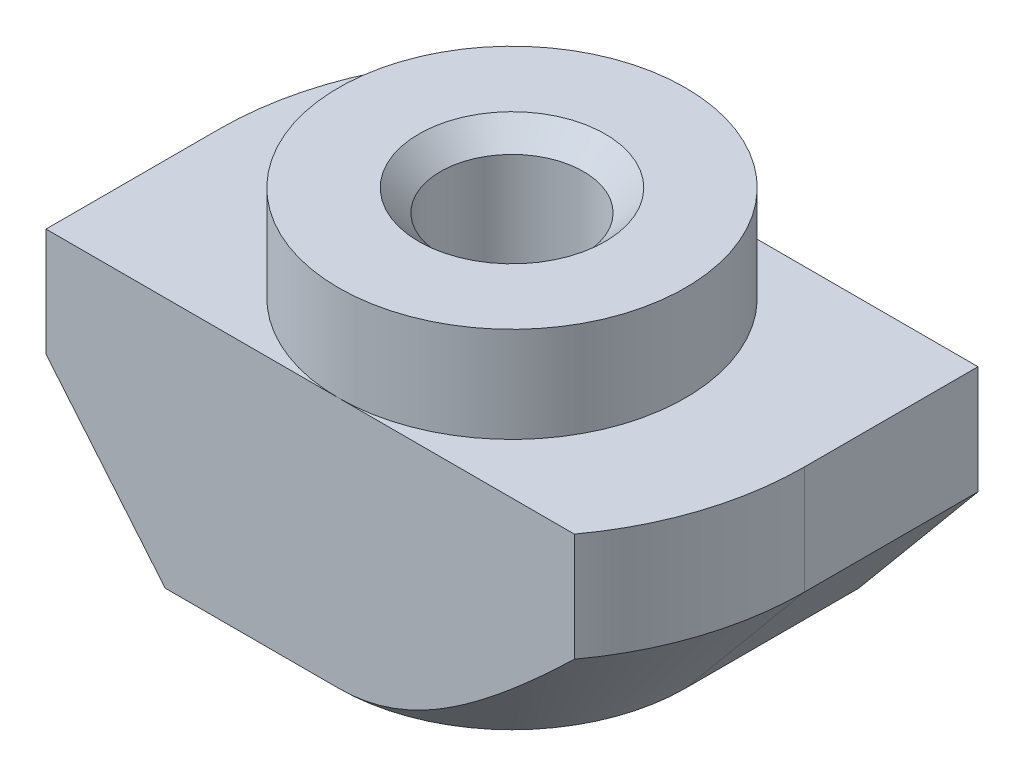
SolidWorks part; units mm, degrees
material "Сталь 20  ГОСТ 1050-2013"
ref_plane "Спереди" through (0, 0, 0) normal (0, 0, 1) x (1, 0, 0)
ref_plane "Сверху" through (0, 0, 0) normal (0, 1, 0) x (1, 0, 0)
ref_plane "Справа" through (0, 0, 0) normal (1, 0, 0) x (0, 0, -1)
sketch "Эскиз1" plane through (0, 0, 0) normal (0, 0, 1) x (1, 0, 0)
  line L0 (4, 0) -> (-4, 0)
  line L1 (-4, 0) -> (-4, -2.2)
  line L2 (-4, -2.2) -> (-6.75, -2.2)
  line L3 (-6.75, -2.2) -> (-6.75, -8)
  line L4 (-6.75, -8) -> (6.75, -8)
  line L5 (0, -8) -> (0, 0) construction
  line L6 (6.75, -2.2) -> (6.75, -8)
  line L7 (4, -2.2) -> (6.75, -2.2)
  line L8 (4, 0) -> (4, -2.2)
  dimension "D1" = 8
  dimension "D2" = 13.5
  dimension "D3" = 8
  dimension "D4" = 2.2
extrude "Бобышка-Вытянуть1" add sketch "Эскиз1" along normal mid plane 8
hole_wizard "Отверстие обработанное метчиком M41" positions "Эскиз2" profile "Эскиз3" tap size "M4" standard "ISO" end condition up to next
sketch "Эскиз2" plane through (0, 0, 0) normal (0, 1, 0) x (1, 0, 0)
  point P0 (0, 0)
sketch "Эскиз3" plane through (0, 0, 0) normal (1, 0, 0) x (0, 0, 1)
  line L0 (0, 0) -> (0, 8)
  line L1 (0, 8) -> (2.15, 8)
  line L2 (1.65, 7.5) -> (1.65, 0.5)
  line L3 (1.65, 0.5) -> (2.15, 0)
  line L5 (2.15, 0) -> (0, 0)
  line L6 (-1.65, 0.5) -> (-2.15, 0) construction
  line L7 (2.15, 8) -> (1.65, 7.5)
  line L8 (-2.15, 8) -> (-1.65, 7.5) construction
  line L11 (0, -6.35) -> (0, 107.95) construction
  dimension "Диаметр проходного сверла" = 3.3
  dimension "Глубина проходного сверла" = 8
  dimension "Диаметр передней зенковки" = 4.3
  dimension "Угол передней зенковки" = 90
  dimension "Диаметр задней зенковки" = 4.3
  dimension "Угол задней зенковки" = 90
cosmetic thread "Отверстие резьбы2" parameters "D2"=4
sketch "Эскиз4" plane through (0, 0, 0) normal (0, 1, 0) x (1, 0, 0)
  line L8 (-4, -4) -> (-4, 4) construction
  circle A2 centre (0, 0) radius 4
extrude "Вырез-Вытянуть1" cut sketch "Эскиз4" against normal up to surface (2.2 mm away) flip side to cut up to face at (-5.375, -2.2, 0)
sketch "Эскиз5" plane through (0, -2.2, 0) normal (0, 1, 0) x (1, 0, 0)
  line L0 (-6.75, 0) -> (-6.75, 4)
  line L1 (-6.75, -4) -> (-6.75, 4) construction
  line L2 (-6.75, 4) -> (-5.4371, 4)
  line L3 (0, 4) -> (-6.75, 4) construction
  line L4 (6.75, 0) -> (6.75, -4)
  line L5 (6.75, -4) -> (6.75, 4) construction
  line L6 (6.75, -4) -> (5.4371, -4)
  line L7 (6.75, -4) -> (0, -4) construction
  arc A0 (-5.4371, 4) -> (-6.75, 0) centre (0, 0) ccw
  arc A2 (6.75, 0) -> (5.4371, -4) centre (0, 0) cw
extrude "Вырез-Вытянуть2" cut sketch "Эскиз5" against normal through all
sketch "Эскиз6" plane through (0, 0, 4) normal (0, 0, 1) x (1, 0, 0)
  line L0 (-6.75, -4.7) -> (-6.75, -8)
  line L1 (-6.75, -2.2) -> (-6.75, -8) construction
  line L2 (-6.75, -8) -> (-4, -8)
  line L3 (-6.75, -8) -> (5.4371, -8) construction
  line L4 (-4, -8) -> (-6.75, -4.7)
  line L5 (0, -2.2) -> (-6.75, -2.2) construction
  line L7 (-4, 0) -> (-4, -2.2) construction
  point P10 (0, 0)
  dimension "D1" = 2.5
sketch "Эскиз7" plane through (0, -8, 0) normal (0, -1, 0) x (1, 0, 0)
  line L0 (0, 6.75) -> (-6.75, 6.75)
  line L1 (-6.75, 6.75) -> (-6.75, 0)
  line L2 (0, -6.75) -> (6.75, -6.75)
  line L3 (6.75, -6.75) -> (6.75, 0)
  arc A0 (-6.75, 0) -> (0, -6.75) centre (0, 0) ccw
  arc A1 (6.75, 0) -> (0, 6.75) centre (0, 0) ccw
sweep "Вырез-По траектории1" cut profiles "Эскиз6" path "Эскиз7"
